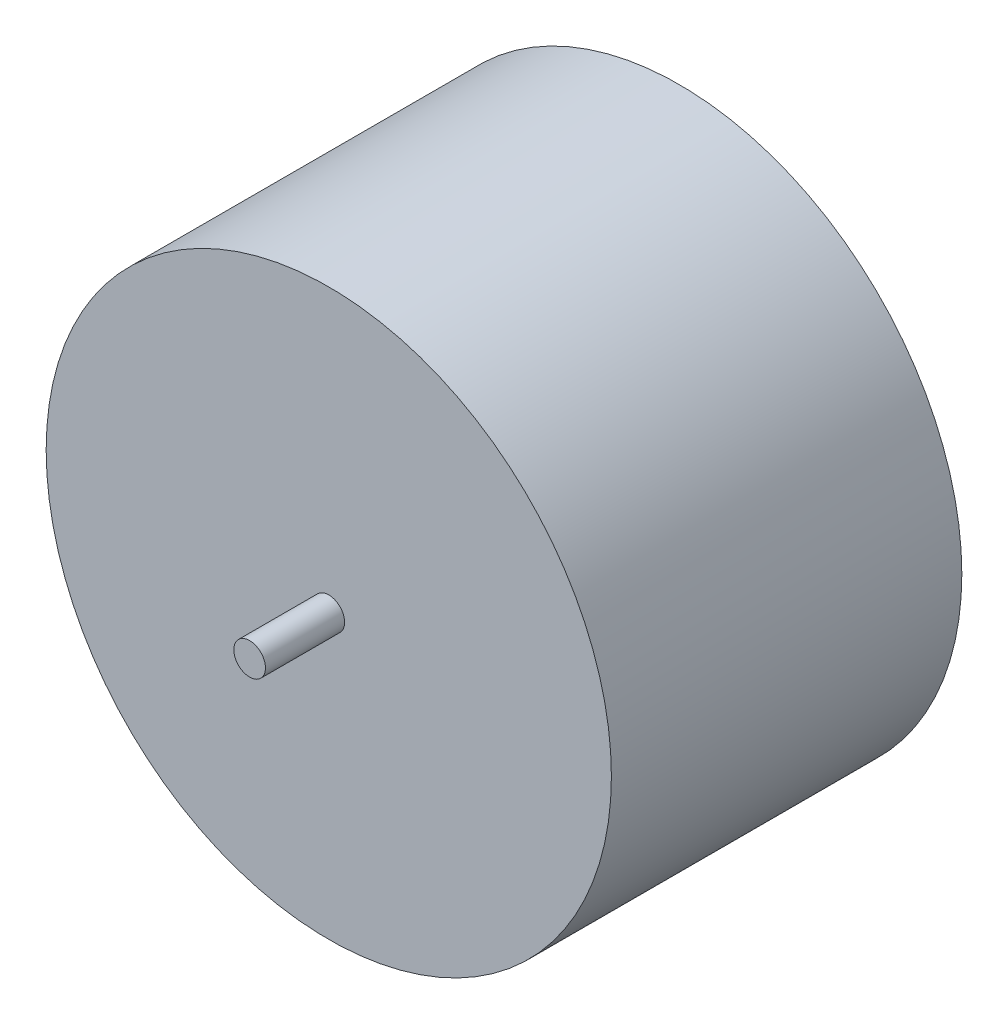
SolidWorks part; units mm, degrees
ref_plane "Front Plane" through (0, 0, 0) normal (0, 0, 1) x (1, 0, 0)
ref_plane "Top Plane" through (0, 0, 0) normal (0, 1, 0) x (1, 0, 0)
ref_plane "Right Plane" through (0, 0, 0) normal (1, 0, 0) x (0, 0, -1)
sketch "Sketch1" plane through (0, 0, 0) normal (0, 0, 1) x (1, 0, 0)
  circle A0 centre (0, 0) radius 125
  dimension "D1" = 250
extrude "Boss-Extrude1" add sketch "Sketch1" along normal blind 155
sketch "Sketch2" plane through (0, 0, 155) normal (0, 0, 1) x (1, 0, 0)
  circle A0 centre (0, 0) radius 7
  dimension "D1" = 14
extrude "Boss-Extrude2" add sketch "Sketch2" along normal blind 35
sketch "Sketch3" plane through (0, 0, 0) normal (0, 0, -1) x (-1, 0, 0)
  circle A0 centre (0, 0) radius 7
  dimension "D1" = 14
extrude "Boss-Extrude3" add sketch "Sketch3" along normal blind 35
